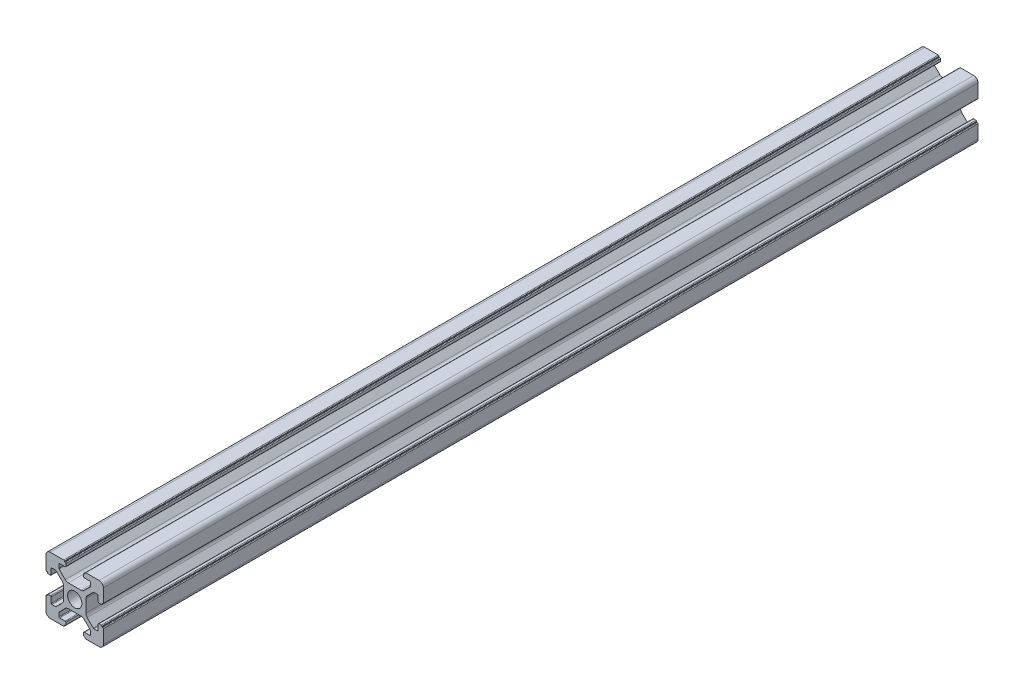
SolidWorks part; units mm, degrees
ref_plane "前视基准面" through (0, 0, 0) normal (0, 0, 1) x (1, 0, 0)
ref_plane "上视基准面" through (0, 0, 0) normal (0, 1, 0) x (1, 0, 0)
ref_plane "右视基准面" through (0, 0, 0) normal (1, 0, 0) x (0, 0, -1)
sketch "草图1" plane through (0, 0, 0) normal (0, 0, 1) x (1, 0, 0)
  line L0 (0, 0) -> (0, 5.5) construction
  line L1 (-8.5023, -10.0023) -> (-3.85, -10.0023)
  line L2 (-10.0023, -8.5023) -> (-10.0023, -3.85)
  line L3 (-8.5023, 10.0023) -> (-3.85, 10.0023)
  line L4 (10.0023, -8.5023) -> (10.0023, -3.85)
  line L5 (-10.0023, -10.0023) -> (10.0023, 10.0023) construction
  line L6 (-10.0023, 10.0023) -> (10.0023, -10.0023) construction
  line L7 (-2.218, -3.9) -> (2.218, -3.9)
  line L8 (-3.9, -2.218) -> (-3.9, 2.218)
  line L9 (-2.218, 3.9) -> (2.218, 3.9)
  line L10 (3.9, -2.218) -> (3.9, 2.218)
  line L11 (-3.9, -3.9) -> (3.9, 3.9) construction
  line L12 (-3.9, 3.9) -> (3.9, -3.9) construction
  line L13 (-5.25, -8.2) -> (-3.35, -8.2)
  line L14 (-8.2, -5.25) -> (-8.2, -3.35)
  line L15 (-5.25, 8.2) -> (-3.35, 8.2)
  line L16 (8.2, -5.25) -> (8.2, -3.35)
  line L17 (-8.2, -8.2) -> (8.2, 8.2) construction
  line L18 (-8.2, 8.2) -> (8.2, -8.2) construction
  line L19 (-7.95, 5.5) -> (-6.6642, 5.5)
  line L20 (0, 0) -> (5.5, 0) construction
  line L23 (-5.5, 7.95) -> (-5.5, 6.6642)
  line L26 (0, 0) -> (-0.5303, 0.5303)
  line L27 (3.2787, 4.3393) -> (5.4268, 6.4874)
  line L28 (0, 0) -> (0.5303, -0.5303)
  line L29 (5.5, 6.6642) -> (5.5, 7.95)
  line L30 (4.3393, 3.2787) -> (6.4874, 5.4268)
  line L31 (6.6642, 5.5) -> (7.95, 5.5)
  line L32 (4.3393, -3.2787) -> (6.4874, -5.4268)
  line L33 (3.2787, -4.3393) -> (5.4268, -6.4874)
  line L34 (-3.2787, -4.3393) -> (-5.4268, -6.4874)
  line L35 (-4.3393, -3.2787) -> (-6.4874, -5.4268)
  line L36 (-4.3393, 3.2787) -> (-6.4874, 5.4268)
  line L37 (-3.2787, 4.3393) -> (-5.4268, 6.4874)
  line L38 (3.1, -8.45) -> (3.1, -9.2523)
  line L39 (8.45, 3.1) -> (9.2523, 3.1)
  line L40 (-5.5, -6.6642) -> (-5.5, -7.95)
  line L41 (-6.6642, -5.5) -> (-7.95, -5.5)
  line L42 (5.5, -6.6642) -> (5.5, -7.95)
  line L43 (6.6642, -5.5) -> (7.95, -5.5)
  line L44 (9.2523, -3.1) -> (8.45, -3.1)
  line L46 (10.0023, 3.85) -> (10.0023, 8.5023)
  line L47 (8.2, 3.35) -> (8.2, 5.25)
  line L48 (-3.1, -9.2523) -> (-3.1, -8.45)
  line L49 (-8.45, -3.1) -> (-9.2523, -3.1)
  line L50 (-9.2523, 3.1) -> (-8.45, 3.1)
  line L51 (-3.1, 8.45) -> (-3.1, 9.2523)
  line L52 (3.1, 9.2523) -> (3.1, 8.45)
  line L53 (3.85, 10.0023) -> (8.5023, 10.0023)
  line L54 (3.35, 8.2) -> (5.25, 8.2)
  line L55 (-10.0023, 3.85) -> (-10.0023, 8.5023)
  line L56 (-8.2, 3.35) -> (-8.2, 5.25)
  line L57 (3.35, -8.2) -> (5.25, -8.2)
  line L58 (3.85, -10.0023) -> (8.5023, -10.0023)
  line L59 (9.7523, -3.6) -> (9.5023, -3.6)
  line L61 (9.7523, 3.6) -> (9.5023, 3.6)
  line L62 (9.5023, -3.6) -> (9.5023, -3.35)
  line L63 (3.6, -9.7523) -> (3.6, -9.5023)
  line L64 (3.35, -9.5023) -> (3.6, -9.5023)
  line L65 (9.5023, 3.35) -> (9.5023, 3.6)
  line L66 (-3.6, -9.5023) -> (-3.35, -9.5023)
  line L67 (-3.6, -9.7523) -> (-3.6, -9.5023)
  line L68 (-9.7523, -3.6) -> (-9.5023, -3.6)
  line L69 (-9.5023, -3.35) -> (-9.5023, -3.6)
  line L70 (-9.5023, 3.6) -> (-9.5023, 3.35)
  line L71 (-9.7523, 3.6) -> (-9.5023, 3.6)
  line L72 (-3.6, 9.7523) -> (-3.6, 9.5023)
  line L73 (-3.35, 9.5023) -> (-3.6, 9.5023)
  line L74 (3.6, 9.5023) -> (3.35, 9.5023)
  line L75 (3.6, 9.7523) -> (3.6, 9.5023)
  circle A0 centre (0, 0) radius 2.5
  arc A1 (10.0023, 8.5023) -> (8.5023, 10.0023) centre (8.5023, 8.5023) ccw
  arc A2 (8.5023, -10.0023) -> (10.0023, -8.5023) centre (8.5023, -8.5023) ccw
  arc A3 (-10.0023, -8.5023) -> (-8.5023, -10.0023) centre (-8.5023, -8.5023) ccw
  arc A4 (-10.0023, 8.5023) -> (-8.5023, 10.0023) centre (-8.5023, 8.5023) cw
  arc A5 (-9.5023, -3.35) -> (-9.2523, -3.1) centre (-9.2523, -3.35) cw
  arc A6 (-9.7523, -3.6) -> (-10.0023, -3.85) centre (-9.7523, -3.85) ccw
  arc A7 (-8.45, -3.1) -> (-8.2, -3.35) centre (-8.45, -3.35) cw
  arc A8 (-7.95, -5.5) -> (-8.2, -5.25) centre (-7.95, -5.25) cw
  arc A9 (-6.4874, -5.4268) -> (-6.6642, -5.5) centre (-6.6642, -5.25) cw
  arc A10 (-5.4268, -6.4874) -> (-5.5, -6.6642) centre (-5.25, -6.6642) ccw
  arc A11 (-5.5, -7.95) -> (-5.25, -8.2) centre (-5.25, -7.95) ccw
  arc A12 (-3.6, -9.7523) -> (-3.85, -10.0023) centre (-3.85, -9.7523) cw
  arc A13 (-3.35, -9.5023) -> (-3.1, -9.2523) centre (-3.35, -9.2523) ccw
  arc A14 (-3.1, -8.45) -> (-3.35, -8.2) centre (-3.35, -8.45) ccw
  arc A15 (3.1, -8.45) -> (3.35, -8.2) centre (3.35, -8.45) cw
  arc A16 (5.5, -7.95) -> (5.25, -8.2) centre (5.25, -7.95) cw
  arc A17 (5.4268, -6.4874) -> (5.5, -6.6642) centre (5.25, -6.6642) cw
  arc A18 (6.4874, -5.4268) -> (6.6642, -5.5) centre (6.6642, -5.25) ccw
  arc A19 (7.95, -5.5) -> (8.2, -5.25) centre (7.95, -5.25) ccw
  arc A20 (8.45, -3.1) -> (8.2, -3.35) centre (8.45, -3.35) ccw
  arc A21 (9.5023, -3.35) -> (9.2523, -3.1) centre (9.2523, -3.35) ccw
  arc A22 (9.7523, -3.6) -> (10.0023, -3.85) centre (9.7523, -3.85) cw
  arc A23 (3.35, -9.5023) -> (3.1, -9.2523) centre (3.35, -9.2523) cw
  arc A24 (3.6, -9.7523) -> (3.85, -10.0023) centre (3.85, -9.7523) ccw
  arc A25 (7.95, 5.5) -> (8.2, 5.25) centre (7.95, 5.25) cw
  arc A26 (8.2, 3.35) -> (8.45, 3.1) centre (8.45, 3.35) ccw
  arc A27 (9.5023, 3.35) -> (9.2523, 3.1) centre (9.2523, 3.35) cw
  arc A28 (9.7523, 3.6) -> (10.0023, 3.85) centre (9.7523, 3.85) ccw
  arc A29 (6.6642, 5.5) -> (6.4874, 5.4268) centre (6.6642, 5.25) ccw
  arc A30 (5.4268, 6.4874) -> (5.5, 6.6642) centre (5.25, 6.6642) ccw
  arc A31 (5.5, 7.95) -> (5.25, 8.2) centre (5.25, 7.95) ccw
  arc A32 (3.1, 8.45) -> (3.35, 8.2) centre (3.35, 8.45) ccw
  arc A33 (3.6, 9.7523) -> (3.85, 10.0023) centre (3.85, 9.7523) cw
  arc A34 (3.35, 9.5023) -> (3.1, 9.2523) centre (3.35, 9.2523) ccw
  arc A35 (-9.7523, 3.6) -> (-10.0023, 3.85) centre (-9.7523, 3.85) cw
  arc A36 (-9.5023, 3.35) -> (-9.2523, 3.1) centre (-9.2523, 3.35) ccw
  arc A37 (-8.45, 3.1) -> (-8.2, 3.35) centre (-8.45, 3.35) ccw
  arc A38 (-8.2, 5.25) -> (-7.95, 5.5) centre (-7.95, 5.25) cw
  arc A39 (-6.4874, 5.4268) -> (-6.6642, 5.5) centre (-6.6642, 5.25) ccw
  arc A40 (-5.4268, 6.4874) -> (-5.5, 6.6642) centre (-5.25, 6.6642) cw
  arc A41 (-5.5, 7.95) -> (-5.25, 8.2) centre (-5.25, 7.95) cw
  arc A42 (-3.1, 8.45) -> (-3.35, 8.2) centre (-3.35, 8.45) cw
  arc A43 (-3.1, 9.2523) -> (-3.35, 9.5023) centre (-3.35, 9.2523) ccw
  arc A44 (-3.6, 9.7523) -> (-3.85, 10.0023) centre (-3.85, 9.7523) ccw
  arc A45 (-4.3393, 3.2787) -> (-3.9, 2.218) centre (-5.4, 2.218) cw
  arc A46 (-3.2787, 4.3393) -> (-2.218, 3.9) centre (-2.218, 5.4) ccw
  arc A47 (3.2787, 4.3393) -> (2.218, 3.9) centre (2.218, 5.4) cw
  arc A48 (4.3393, 3.2787) -> (3.9, 2.218) centre (5.4, 2.218) ccw
  arc A49 (4.3393, -3.2787) -> (3.9, -2.218) centre (5.4, -2.218) cw
  arc A50 (3.2787, -4.3393) -> (2.218, -3.9) centre (2.218, -5.4) ccw
  arc A51 (-4.3393, -3.2787) -> (-3.9, -2.218) centre (-5.4, -2.218) ccw
  arc A52 (-2.218, -3.9) -> (-3.2787, -4.3393) centre (-2.218, -5.4) ccw
  point P0 (0, 0)
  point P7 (10.0023, 0)
  point P62 (0, 0)
  point P76 (0, 0)
  point P92 (-8.2, -5.5)
  point P99 (0, 0)
  point P106 (-5.5, -8.2)
  point P117 (5.5, -8.2)
  point P124 (8.2, -5.5)
  point P137 (8.2, 5.5)
  point P140 (8.2, 3.1)
  point P147 (6.5607, 5.5)
  point P152 (5.5, 8.2)
  point P167 (-8.2, 5.5)
  point P174 (-5.5, 8.2)
  dimension "D1" = 1.5
  dimension "D5" = 0.25
  dimension "D6" = 1.5
  dimension "D2" = 4
  dimension "D3" = 4
  dimension "D4" = 4
extrude "凸台-拉伸1" add sketch "草图1" along normal blind 304.8 contours A52 L7 A50 L33 A17 L42 A16 L57 A15 L38 A23 L64 L63 A24 L58 A2 L4 A22 L59 L62 A21 L44 A20 L16 A19 L43 A18 L32 A49 L10 A48 L30 A29 L31 A25 L47 A26 L39 A27 L65 L61 A28 L46 A1 L53 A33 L75 L74 A34 L52 A32
ref_plane "Plane1" through (0, 0, 152.4) normal (0, 0, 1) x (1, 0, 0)
